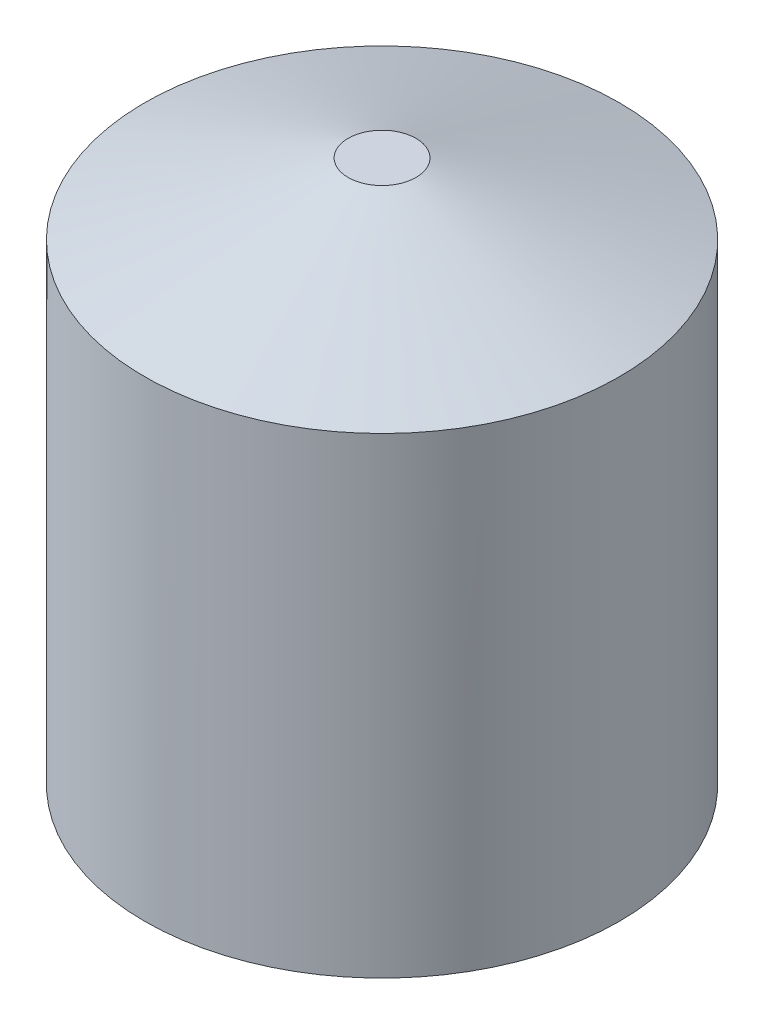
SolidWorks part; units mm, degrees
ref_plane "Front Plane" through (0, 0, 0) normal (0, 0, 1) x (1, 0, 0)
ref_plane "Top Plane" through (0, 0, 0) normal (0, 1, 0) x (1, 0, 0)
ref_plane "Right Plane" through (0, 0, 0) normal (1, 0, 0) x (0, 0, -1)
sketch "Sketch1" plane through (0, 0, 0) normal (0, 1, 0) x (1, 0, 0)
  circle A0 centre (0, 0) radius 1400
  dimension "D1" = 2800
extrude "Boss-Extrude1" add sketch "Sketch1" along normal blind 3200
sketch "Sketch2" plane through (0, 0, 0) normal (0, 0, 1) x (1, 0, 0)
  line L0 (200, 3200) -> (1990.7424, 2576.3114)
  line L2 (1990.7424, 2576.3114) -> (1990.7424, 3200)
  line L3 (1990.7424, 3200) -> (200, 3200)
  line L4 (0, 4385.8597) -> (0, -1964.8441) construction
  line L5 (1400, 3200) -> (-1400, 3200) construction
  point P2 (200.084, 3200)
  dimension "D1" = 200
revolve "Cut-Revolve2" cut sketch "Sketch2" angle 360 about L4
